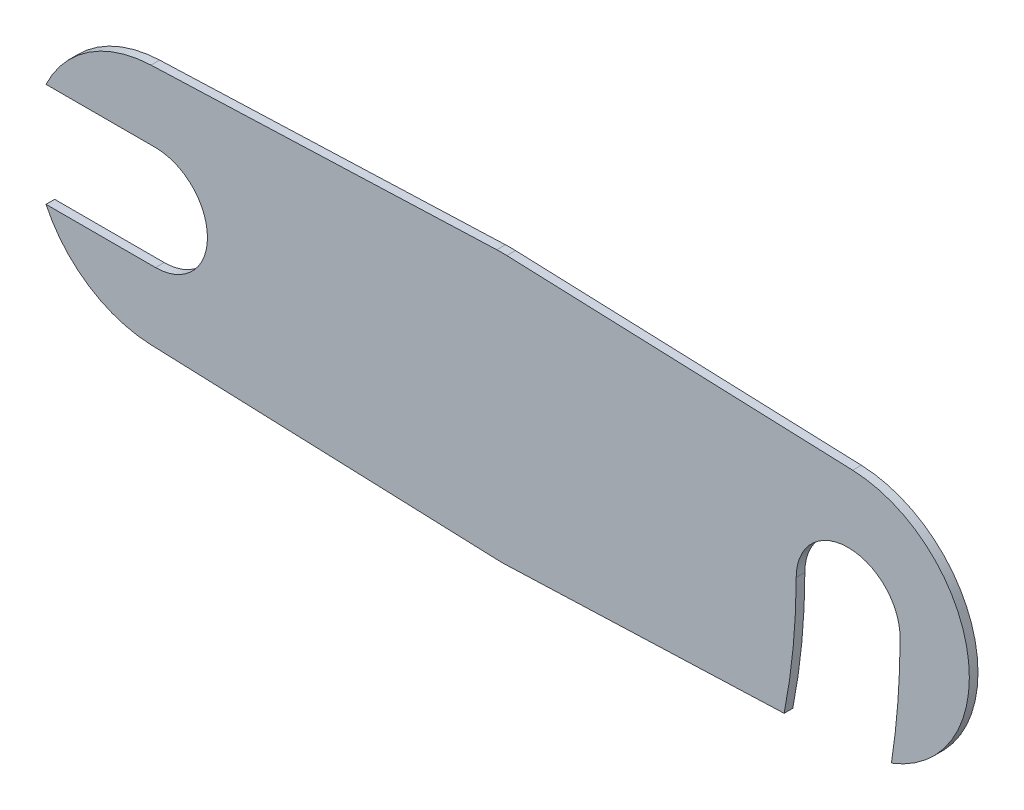
SolidWorks part; units mm, degrees
ref_plane "Płaszczyzna XY" through (0, 0, 0) normal (0, 0, 1) x (1, 0, 0)
ref_plane "Płaszczyzna XZ" through (0, 0, 0) normal (0, 1, 0) x (1, 0, 0)
ref_plane "Płaszczyzna YZ" through (0, 0, 0) normal (1, 0, 0) x (0, 0, -1)
sketch "Szkic1" plane through (0, 0, 0) normal (0, 0, 1) x (1, 0, 0)
  line L0 (-0.2906, 7.7445) -> (-20.2625, 6.9951)
  line L1 (-0.2906, -7.7445) -> (-20.2625, -6.9951)
  line L2 (0.2906, 7.7445) -> (20.2625, 6.9951)
  line L3 (0, 0) -> (0, -3.6778) construction
  line L10 (0.2906, -7.7445) -> (20.2625, -6.9951)
  arc A0 (-0.2906, -7.7445) -> (0.2906, -7.7445) centre (0, 0) ccw
  arc A2 (-20.2625, 6.9951) -> (-20.2625, -6.9951) centre (-20, 0) ccw
  arc A3 (20.2625, -6.9951) -> (20.2625, 6.9951) centre (20, 0) ccw
  arc A4 (0.2906, 7.7445) -> (-0.2906, 7.7445) centre (0, 0) ccw
  circle A5 centre (-20, 0) radius 3
  circle A10 centre (20, 0) radius 3
  dimension "D2" = 15.5
  dimension "D3" = 14
  dimension "D4" = 6
  dimension "D1" = 40
extrude "Dodanie-wyciągnięcie1" add sketch "Szkic1" along normal blind 0.5
sketch "Szkic2" plane through (0, 0, 0.5) normal (0, 0, 1) x (1, 0, 0)
  line L0 (-20, 3) -> (-26.3246, 3)
  line L1 (-20, -3) -> (-26.3246, -3)
  circle A0 centre (-20, 0) radius 3 construction
  arc A1 (-20.2625, 6.9951) -> (-20.2625, -6.9951) centre (-20, 0) ccw construction
  arc A2 (-26.3246, -3) -> (-26.3246, 3) centre (-20, 0) cw
  arc A3 (-20, -3) -> (-20, 3) centre (-20, 0) cw
extrude "Wytnij-wyciągnięcie1" cut sketch "Szkic2" against normal through all
sketch "Szkic3" plane through (0, 0, 0.5) normal (0, 0, 1) x (1, 0, 0)
  line L0 (0.2906, -7.7445) -> (20.2625, -6.9951) construction
  line L1 (16.3038, -7.1436) -> (20.2625, -6.9951)
  arc A0 (17, 0) -> (16.3038, -7.1436) centre (-20, 0) cw
  circle A1 centre (20, 0) radius 3 construction
  arc A2 (23, 0) -> (22.5, -6.5383) centre (-20, 0) cw
  arc A3 (20.2625, -6.9951) -> (20.2625, 6.9951) centre (20, 0) ccw construction
  arc A4 (17, 0) -> (23, 0) centre (20, 0) ccw
  arc A5 (20.2625, -6.9951) -> (22.5, -6.5383) centre (20, 0) ccw
  line M5 (0.2906, -7.7445) -> (20.2625, -6.9951)
  arc M6 (20.2625, -6.9951) -> (20.2625, 6.9951) centre (20, 0) ccw
  circle M13 centre (20, 0) radius 3
extrude "Wytnij-wyciągnięcie3" cut sketch "Szkic3" against normal through all contours A2 A0 M13 M5 M6
